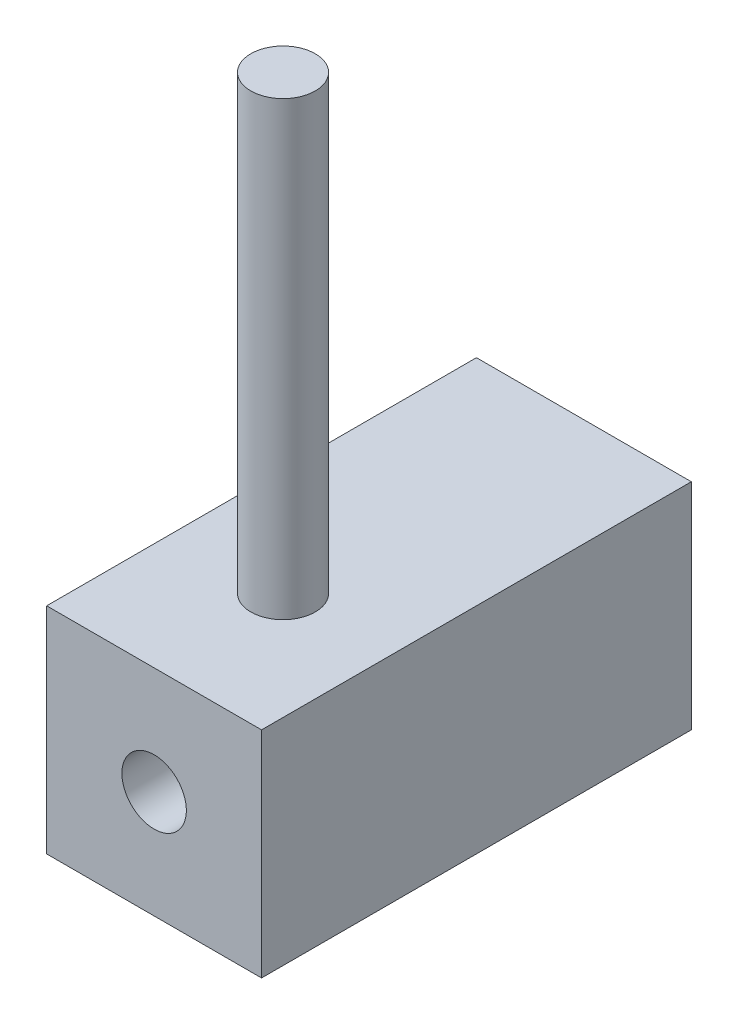
SolidWorks part; units mm, degrees
ref_plane "Front Plane" through (0, 0, 0) normal (0, 0, 1) x (1, 0, 0)
ref_plane "Top Plane" through (0, 0, 0) normal (0, 1, 0) x (1, 0, 0)
ref_plane "Right Plane" through (0, 0, 0) normal (1, 0, 0) x (0, 0, -1)
sketch "Sketch1" plane through (0, 0, 0) normal (0, 1, 0) x (1, 0, 0)
  line L1 (-4.9718, 2.5141) -> (5.0282, 2.5141)
  line L2 (-4.9718, 2.5141) -> (-4.9718, -17.4859)
  line L3 (-4.9718, -17.4859) -> (5.0282, -17.4859)
  line L4 (5.0282, 2.5141) -> (5.0282, -17.4859)
  dimension "D1" = 10
  dimension "D2" = 20
extrude "Boss-Extrude1" add sketch "Sketch1" along normal blind 10
sketch "Sketch2" plane through (0, 10, 0) normal (0, 1, 0) x (1, 0, 0)
  line L0 (5.0282, -17.4859) -> (5.0282, 2.5141) construction
  line L1 (-4.9718, -17.4859) -> (5.0282, -17.4859) construction
  line L2 (5.0282, 2.5141) -> (-4.9718, 2.5141) construction
  circle A0 centre (0.0282, -11.4859) radius 1.5
  dimension "D1" = 3
  dimension "D2" = 5
  dimension "D3" = 6
  dimension "D4" = 14
sketch "Sketch3" plane through (0, 0, -2.5141) normal (0, 0, -1) x (-1, 0, 0)
  line L0 (4.9718, 10) -> (4.9718, 0) construction
  line L1 (-5.0282, 10) -> (4.9718, 10) construction
  circle A0 centre (-0.0282, 5) radius 1.5
  point P4 (-0.0282, 10)
  dimension "D1" = 3
  dimension "D2" = 5
  dimension "D3" = 5
extrude "Cut-Extrude1" cut sketch "Sketch3" against normal blind 21
extrude "Boss-Extrude2" add sketch "Sketch2" along normal blind 21
